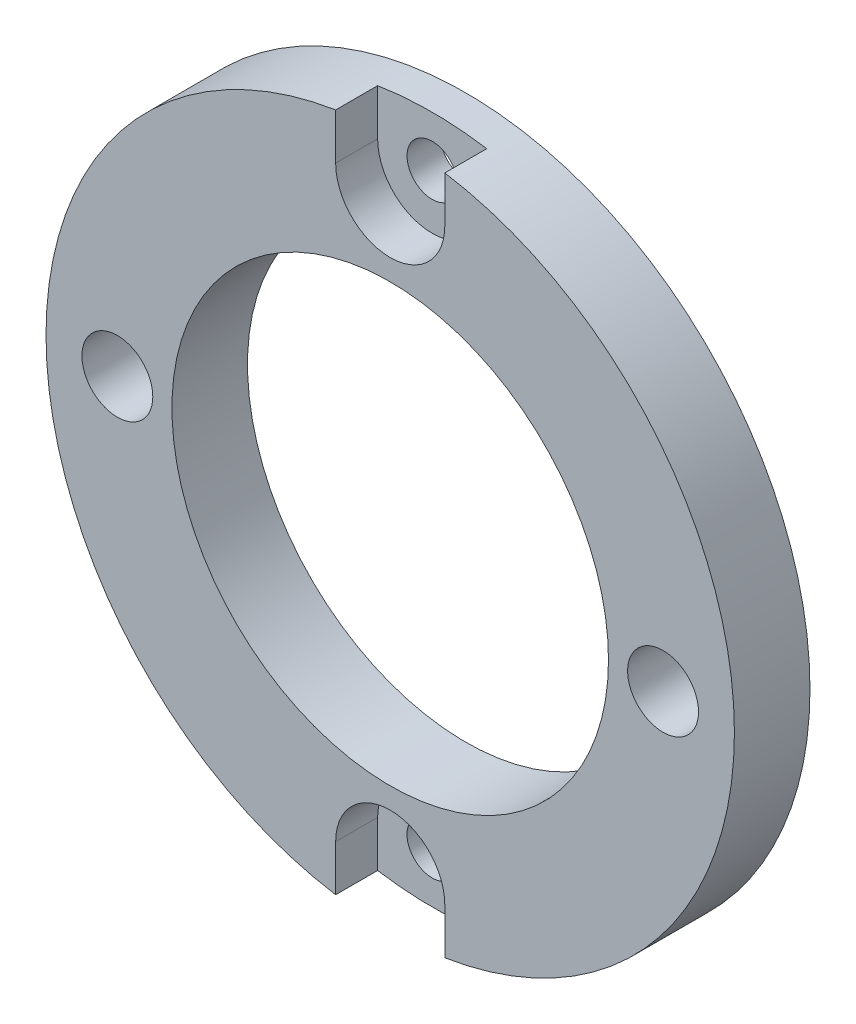
SolidWorks part; units mm, degrees
ref_plane "Plan de face" through (0, 0, 0) normal (0, 0, 1) x (1, 0, 0)
ref_plane "Plan de dessus" through (0, 0, 0) normal (0, 1, 0) x (1, 0, 0)
ref_plane "Plan de droite" through (0, 0, 0) normal (1, 0, 0) x (0, 0, -1)
sketch "Esquisse1" plane through (0, 0, 0) normal (0, 0, 1) x (1, 0, 0)
  circle A0 centre (0, 0) radius 20.5
  circle A1 centre (0, 0) radius 13
  dimension "D1" = 41
  dimension "D2" = 26
extrude "Boss.-Extru.1" add sketch "Esquisse1" along normal blind 4.5
sketch "Esquisse2" plane through (0, 0, 4.5) normal (0, 0, 1) x (1, 0, 0)
  line L0 (0, 7.8152) -> (0, -9.0227) construction
  line L1 (7.3791, 0) -> (-8.05, 0) construction
  circle A0 centre (0, 17.5) radius 1.5
  circle A1 centre (16.25, 0) radius 2.11
  circle A2 centre (0, -17.5) radius 1.5
  circle A3 centre (-16.25, 0) radius 2.11
  dimension "D3" = 3
  dimension "D4" = 4.22
  dimension "D1" = 17.5
  dimension "D2" = 16.25
extrude "Enlèv. mat.-Extru.1" cut sketch "Esquisse2" against normal up to next
sketch "Esquisse3" plane through (0, 0, 4.5) normal (0, 0, 1) x (1, 0, 0)
  line L0 (-3.25, 17.5) -> (-3.25, 27.5)
  line L1 (-3.25, 27.5) -> (3.25, 27.5)
  line L2 (3.25, 27.5) -> (3.25, 17.5)
  line L3 (-5.0715, 0) -> (5.313, 0) construction
  line L4 (-3.25, -27.5) -> (3.25, -27.5)
  line L5 (3.25, -27.5) -> (3.25, -17.5)
  line L6 (-3.25, -17.5) -> (-3.25, -27.5)
  arc A0 (-3.25, 17.5) -> (3.25, 17.5) centre (0, 17.5) ccw
  arc A1 (-3.25, -17.5) -> (3.25, -17.5) centre (0, -17.5) cw
  dimension "D1" = 3.25
  dimension "D2" = 10
extrude "Enlèv. mat.-Extru.2" cut sketch "Esquisse3" against normal blind 2.5
